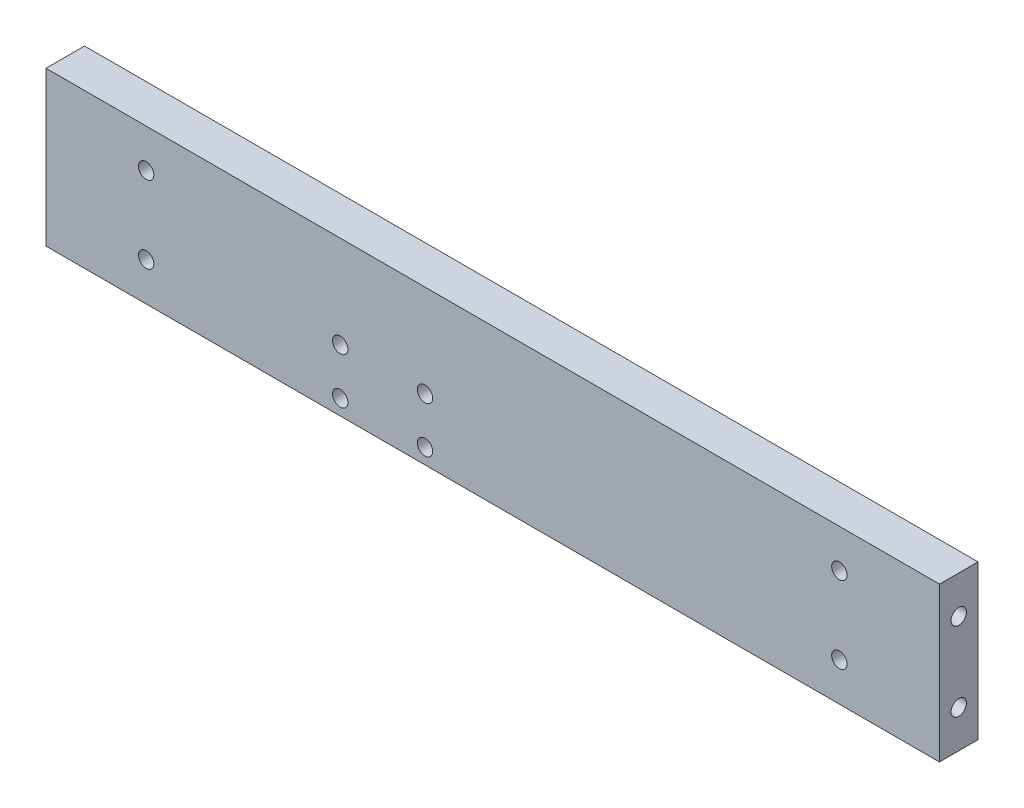
SolidWorks part; units mm, degrees
ref_plane "Front Plane" through (0, 0, 0) normal (0, 0, 1) x (1, 0, 0)
ref_plane "Top Plane" through (0, 0, 0) normal (0, 1, 0) x (1, 0, 0)
ref_plane "Right Plane" through (0, 0, 0) normal (1, 0, 0) x (0, 0, -1)
sketch "Sketch1" plane through (0, 0, 0) normal (0, 0, 1) x (1, 0, 0)
  line L1 (-58, 10) -> (58, 10)
  line L2 (-58, 10) -> (-58, -10)
  line L3 (-58, -10) -> (58, -10)
  line L4 (58, 10) -> (58, -10)
  line L5 (-58, 10) -> (58, -10) construction
  line L6 (-58, -10) -> (58, 10) construction
  line L11 (-15.5, 15.5) -> (15.5, -15.5) construction
  line L12 (-15.5, -15.5) -> (15.5, 15.5) construction
  point P0 (0, 0)
  dimension "D1" = 20
  dimension "D2" = 116
  dimension "D4" = 31
  dimension "D5" = 31
extrude "Boss-Extrude2" add sketch "Sketch1" along normal blind 5
ref_plane "Plane1" through (58, 0, 0) normal (1, 0, 0) x (0, 0, -1)
sketch "Sketch4" plane through (58, 0, 0) normal (1, 0, 0) x (0, 0, -1)
  line L0 (-5, 0) -> (0, 0)
  line L1 (-5, 10) -> (-5, -10) construction
  line L2 (0, 11) -> (0, -11) construction
  circle A0 centre (-2.5, 5.12) radius 1
  circle A1 centre (-2.5, -5.12) radius 1
  dimension "D1" = 2
  dimension "D2" = 5.12
  dimension "D3" = 2.5
extrude "Cut-Extrude1" cut sketch "Sketch4" against normal blind 10 contours A1 | A0
ref_plane "Plane2" through (58, 0, 0) normal (1, 0, 0) x (0, 0, -1)
ref_plane "Plane3" through (-58, 0, 0) normal (-1, 0, 0) x (0, 0, 1)
sketch "Sketch6" plane through (-58, 0, 0) normal (-1, 0, 0) x (0, 0, 1)
  line L0 (0, 0) -> (5, 0)
  line L1 (0, 10) -> (0, -10) construction
  line L2 (5, 10) -> (5, -10) construction
  circle A0 centre (2.5, 5) radius 1
  circle A1 centre (2.5, -5) radius 1
  dimension "D2" = 2
  dimension "D1" = 5
  dimension "D3" = 2.5
extrude "Cut-Extrude2" cut sketch "Sketch6" against normal blind 5 contours A0 | A1
ref_plane "Plane4" through (0, 0, 0) normal (0, 0, -1) x (-1, 0, 0)
sketch "Sketch7" plane through (0, 0, 0) normal (0, 0, -1) x (-1, 0, 0)
  line L0 (58, 10) -> (-58, 10) construction
  line L1 (50, -10) -> (-50, -10)
  line L2 (50, -10) -> (50, 10)
  line L3 (50, 10) -> (-50, 10)
  line L4 (-50, -10) -> (-50, 10)
  line L5 (50, -10) -> (-50, 10) construction
  line L6 (50, 10) -> (-50, -10) construction
  line L7 (-50, 0) -> (50, 0)
  line L8 (0, 10) -> (0, -10)
  circle A0 centre (-45, 5) radius 1
  circle A1 centre (-45, -5) radius 1
  circle A2 centre (45, 5) radius 1
  circle A3 centre (45, -5) radius 1
  point P0 (0, 0)
  dimension "D2" = 2
  dimension "D3" = 5
  dimension "D4" = 5
  dimension "D1" = 100
extrude "Cut-Extrude3" cut sketch "Sketch7" against normal through all contours A0 | A1 | A3 | A2
ref_plane "Plane5" through (0, 0, 0) normal (0, 0, -1) x (-1, 0, 0)
sketch "Sketch8" plane through (0, 0, 0) normal (0, 0, -1) x (-1, 0, 0)
  line L0 (58, 10) -> (-58, 10) construction
  line L1 (6.8, 10) -> (21.8, 10)
  line L2 (6.8, 10) -> (6.8, 0)
  line L3 (6.8, 0) -> (21.8, 0)
  line L4 (21.8, 10) -> (21.8, 0)
  line L5 (2.75, 0) -> (-2.75, 0) construction
  line L6 (58, -2.75) -> (58, 2.75) construction
  line L7 (14.3, 10) -> (14.3, 0)
  line L8 (14.3, 0) -> (6.8, 5)
  line L9 (6.8, 5) -> (21.8, 5)
  circle A0 centre (19.8, 8) radius 1
  circle A1 centre (8.8, 8) radius 1
  circle A2 centre (8.8, 2) radius 1
  circle A3 centre (19.8, 2) radius 1
  circle A4 centre (19.8, -8) radius 1
  circle A5 centre (19.8, -2) radius 1
  circle A6 centre (8.8, -2) radius 1
  circle A7 centre (8.8, -8) radius 1
  dimension "D3" = 2
  dimension "D4" = 2
  dimension "D5" = 2
  dimension "D1" = 36.2
  dimension "D2" = 15
extrude "Cut-Extrude4" cut sketch "Sketch8" against normal through all contours A6 | A7 | A4 | A5
